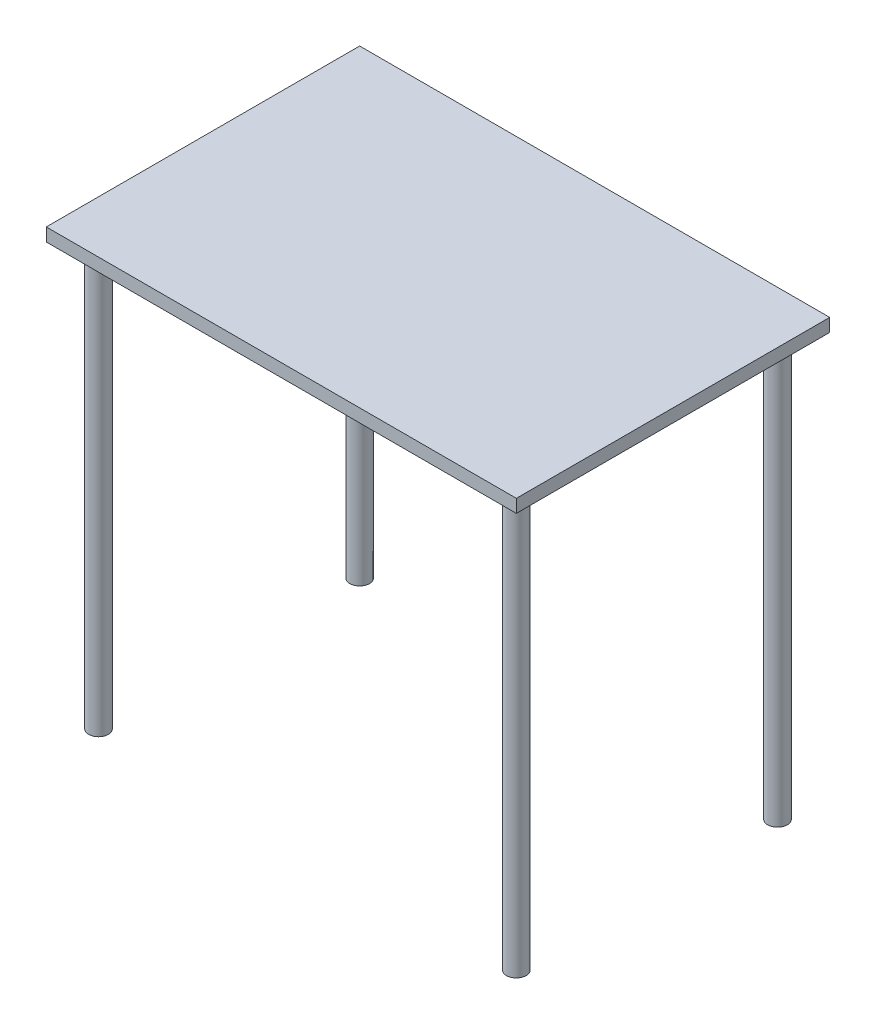
SolidWorks part; units mm, degrees
ref_plane "Front Plane" through (0, 0, 0) normal (0, 0, 1) x (1, 0, 0)
ref_plane "Top Plane" through (0, 0, 0) normal (0, 1, 0) x (1, 0, 0)
ref_plane "Right Plane" through (0, 0, 0) normal (1, 0, 0) x (0, 0, -1)
sketch "Sketch3" plane through (0, 0, 0) normal (0, 1, 0) x (1, 0, 0)
  line L1 (0, 0) -> (914.4, 0)
  line L2 (0, 0) -> (0, 609.6)
  line L3 (0, 609.6) -> (914.4, 609.6)
  line L4 (914.4, 0) -> (914.4, 609.6)
  dimension "D1" = 914.4
  dimension "D2" = 609.6
extrude "Table" add sketch "Sketch3" along normal blind 25.4
sketch "Sketch4" plane through (0, 0, 0) normal (0, -1, 0) x (1, 0, 0)
  line L0 (50.8, -50.8) -> (0, -50.8) construction
  line L1 (0, 0) -> (50.8, 0) construction
  line L2 (0, 0) -> (0, -50.8) construction
  line L4 (50.8, 0) -> (50.8, -50.8) construction
  line L5 (0, -609.6) -> (50.8, -609.6) construction
  line L6 (0, -609.6) -> (0, -558.8) construction
  line L7 (0, -558.8) -> (50.8, -558.8) construction
  line L8 (50.8, -609.6) -> (50.8, -558.8) construction
  line L9 (914.4, -609.6) -> (863.6, -609.6) construction
  line L10 (914.4, -609.6) -> (914.4, -558.8) construction
  line L11 (914.4, -558.8) -> (863.6, -558.8) construction
  line L12 (863.6, -609.6) -> (863.6, -558.8) construction
  line L13 (914.4, 0) -> (863.6, 0) construction
  line L14 (914.4, 0) -> (914.4, -50.8) construction
  line L15 (914.4, -50.8) -> (863.6, -50.8) construction
  line L16 (863.6, 0) -> (863.6, -50.8) construction
  circle A0 centre (50.8, -50.8) radius 19.05
  circle A1 centre (863.6, -50.8) radius 19.05
  circle A2 centre (50.8, -558.8) radius 19.05
  circle A3 centre (863.6, -558.8) radius 19.05
  dimension "D1" = 38.1
  dimension "D2" = 50.8
extrude "Legs" add sketch "Sketch4" along normal offset from surface (820.0644 mm away) 845.4644 up to face at (457.2, 25.4, -304.8)
sketch "Sketch5" plane through (0, 0, 0) normal (0, 0, 1) x (1, 0, 0)
  line L0 (0, 43.5356) -> (0, -820.0644) construction
  line L1 (0, 25.4) -> (0, 0) construction
  line L2 (31.75, -820.0644) -> (69.85, -820.0644) construction
  line L3 (0, 43.5356) -> (0, 62.5856) construction
  line L4 (0, 62.5856) -> (12.7, 62.5856) construction
  line L5 (12.7, 62.5856) -> (12.7, 59.4106) construction
  line L6 (12.7, 59.4106) -> (25.4, 59.4106) construction
  line L7 (25.4, 59.4106) -> (25.4, 25.4106) construction
  line L8 (25.4, 25.4106) -> (38.1, 25.4106) construction
  line L9 (38.1, 25.4106) -> (38.1, 0.0106) construction
  dimension "D1" = 863.6
  dimension "D2" = 19.05
  dimension "D3" = 3.175
  dimension "D4" = 34
  dimension "D5" = 25.4
  dimension "D6" = 12.7
